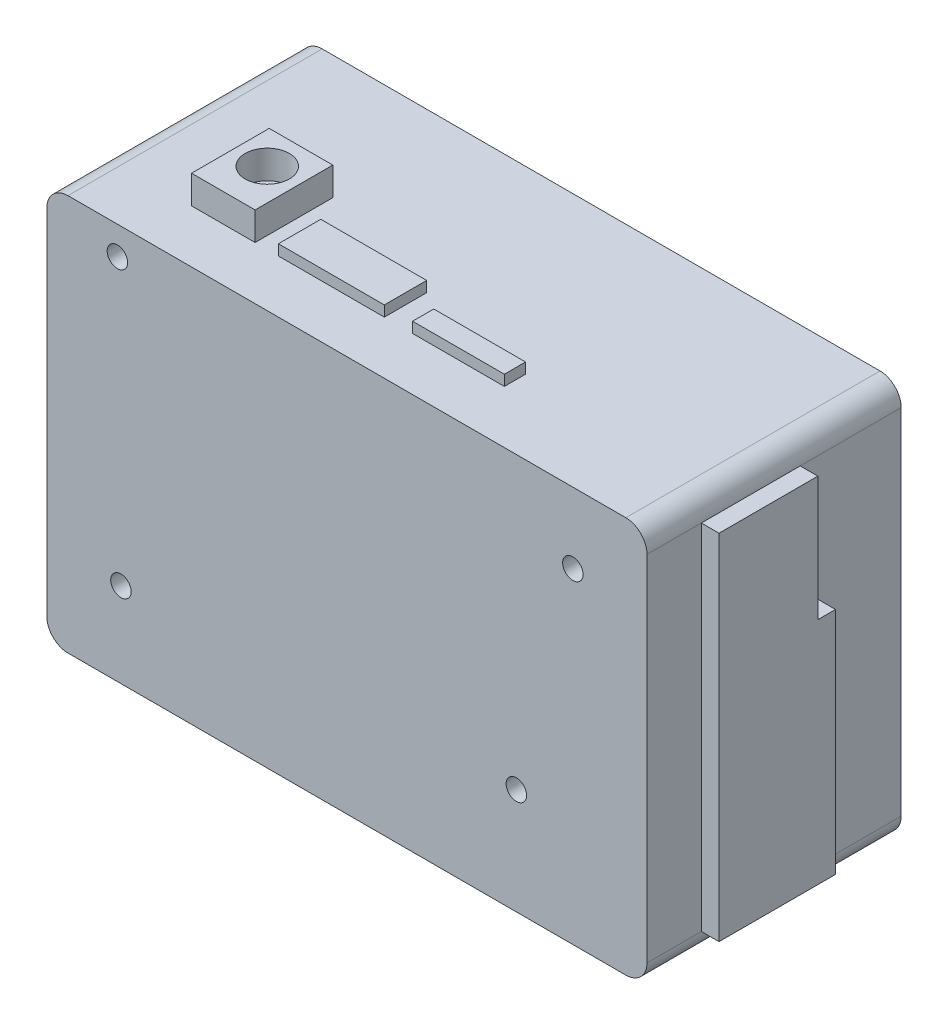
SolidWorks part; units mm, degrees
material "ABS"
ref_plane "Front" through (0, 0, 0) normal (0, 0, 1) x (1, 0, 0)
ref_plane "Top" through (0, 0, 0) normal (0, 1, 0) x (1, 0, 0)
ref_plane "Right" through (0, 0, 0) normal (1, 0, 0) x (0, 0, -1)
sketch "Sketch1" plane through (0, 0, 0) normal (0, 0, 1) x (1, 0, 0)
  line L1 (42.5, -28.05) -> (-42.5, -28.05)
  line L2 (42.5, -28.05) -> (42.5, 28.05)
  line L3 (42.5, 28.05) -> (-42.5, 28.05)
  line L4 (-42.5, -28.05) -> (-42.5, 28.05)
  line L5 (42.5, -28.05) -> (-42.5, 28.05) construction
  line L6 (42.5, 28.05) -> (-42.5, -28.05) construction
  circle A0 centre (-32.5, 24.05) radius 1.45
  circle A1 centre (-32, -16.05) radius 1.45
  circle A2 centre (32, 18.05) radius 1.45
  circle A3 centre (24, -13.05) radius 1.45
  point P0 (0, 0)
  dimension "D3" = 4
  dimension "D4" = 10
  dimension "D5" = 2.9
  dimension "D6" = 12
  dimension "D7" = 10
  dimension "D8" = 10.5
  dimension "D9" = 15
  dimension "D10" = 18.5
  dimension "D11" = 10.5
  dimension "D1" = 56.1
  dimension "D2" = 85
extrude "Boss-Extrude1" add sketch "Sketch1" along normal blind 36
fillet "Fillet1" radius 3 4 edges at (42.5, 28.05, 18) (42.5, -28.05, 18) (-42.5, -28.05, 18) (-42.5, 28.05, 18)
sketch "Sketch2" plane through (0, 0, 0) normal (0, 0, -1) x (-1, 0, 0)
  circle A0 centre (0, 0) radius 20.26
extrude "Cut-Extrude1" [suppressed] cut sketch "Sketch2" against normal through all
sketch "Sketch3" plane through (42.5, 0, 0) normal (1, 0, 0) x (0, 0, -1)
  line L1 (-14.3, 25.55) -> (-28.3, 25.55)
  line L2 (-14.3, 25.55) -> (-14.3, -26.55)
  line L3 (-14.3, -26.55) -> (-28.3, -26.55)
  line L4 (-28.3, 25.55) -> (-28.3, -26.55)
  line L5 (0, 28.05) -> (-36, 28.05) construction
  line L6 (-36, -28.05) -> (0, -28.05) construction
  line L10 (-36, -25.05) -> (-36, 25.05) construction
  line L11 (-14.3, -26.55) -> (-11.8, -26.55)
  line L12 (-11.8, -26.55) -> (-11.8, 7.45)
  line L13 (-11.8, 7.45) -> (-14.3, 7.45)
  line M7 (0, 25.05) -> (-36, 25.05)
  line M9 (-36, -25.05) -> (0, -25.05)
  dimension "D1" = 7.7
  dimension "D2" = 2.5
  dimension "D3" = 1.5
  dimension "D4" = 14
  dimension "D7" = 2.5
  dimension "D8" = 34
extrude "Boss-Extrude2" add sketch "Sketch3" along normal blind 2.5 contours L4 L2 M7 M9 | L12 L13 L2 M9
sketch "Sketch5" plane through (0, 0, 0) normal (0, 0, -1) x (-1, 0, 0)
  line L1 (-35.6542, 26.4562) -> (36.3723, 26.4562)
  line L2 (-35.6542, 26.4562) -> (-35.6542, -20.2415)
  line L3 (-35.6542, -20.2415) -> (36.3723, -20.2415)
  line L4 (36.3723, 26.4562) -> (36.3723, -20.2415)
extrude "Boss-Extrude3" add sketch "Sketch5" against normal blind 2.5
sketch "Sketch6" plane through (0, 28.05, 0) normal (0, 1, 0) x (1, 0, 0)
  line L0 (39.5, -36) -> (-39.5, -36) construction
  line L1 (-29.5, -17.5) -> (-20.5, -17.5)
  line L2 (-29.5, -17.5) -> (-29.5, -28.5)
  line L3 (-29.5, -28.5) -> (-20.5, -28.5)
  line L4 (-20.5, -17.5) -> (-20.5, -28.5)
  line L5 (-42.5, -36) -> (-42.5, 0) construction
  circle A0 centre (-25, -22.2803) radius 3.1337
  point P7 (-25, -17.5)
  dimension "D1" = 11
  dimension "D2" = 9
  dimension "D3" = 7.5
  dimension "D4" = 13
extrude "Boss-Extrude4" add sketch "Sketch6" along normal blind 4
sketch "Sketch8" plane through (0, 28.05, 0) normal (0, 1, 0) x (1, 0, 0)
  line L0 (-29.5, -28.5) -> (-20.5, -28.5) construction
  line L1 (-17.2, -22.5) -> (-2.2, -22.5)
  line L2 (-17.2, -22.5) -> (-17.2, -28.5)
  line L3 (-17.2, -28.5) -> (-2.2, -28.5)
  line L4 (-2.2, -22.5) -> (-2.2, -28.5)
  line L5 (-20.5, -28.5) -> (-20.5, -17.5) construction
  line L8 (1.8, -25.5) -> (14.8, -25.5)
  line L9 (1.8, -25.5) -> (1.8, -28.5)
  line L10 (1.8, -28.5) -> (14.8, -28.5)
  line L11 (14.8, -25.5) -> (14.8, -28.5)
  dimension "D1" = 6
  dimension "D2" = 15
  dimension "D3" = 3.3
  dimension "D4" = 13
  dimension "D5" = 3
  dimension "D6" = 4
extrude "Boss-Extrude5" add sketch "Sketch8" along normal blind 1.5
